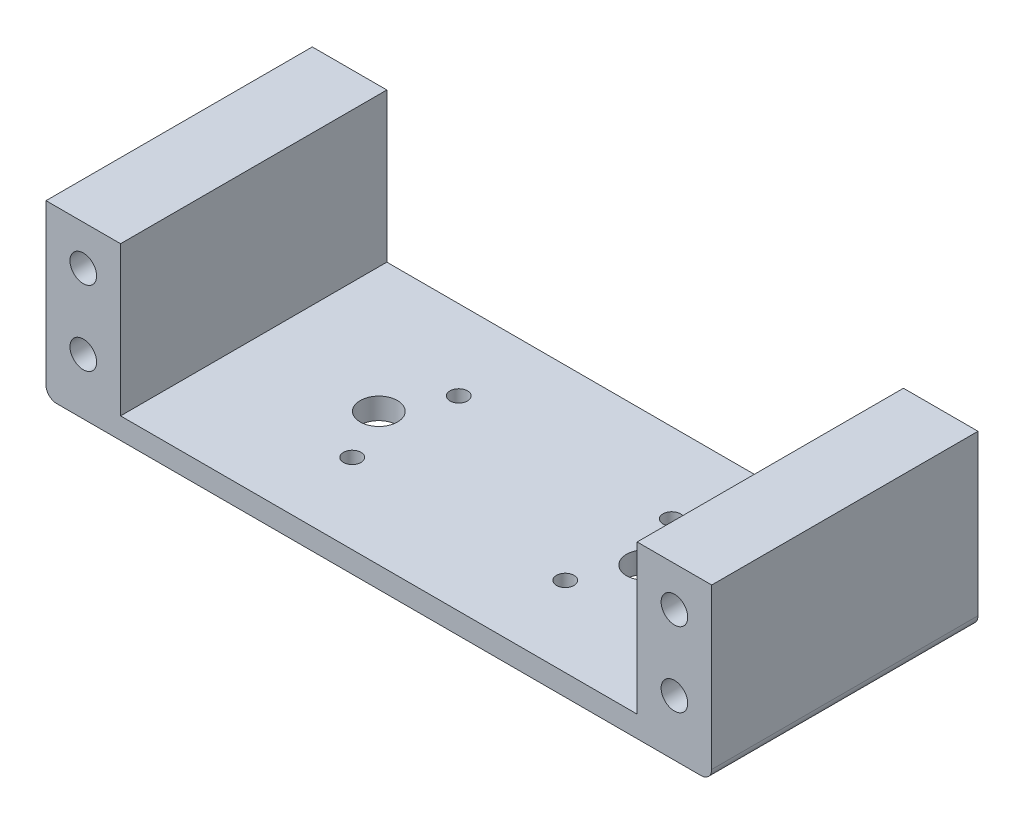
SolidWorks part; units mm, degrees
ref_plane "Front Plane" through (0, 0, 0) normal (0, 0, 1) x (1, 0, 0)
ref_plane "Top Plane" through (0, 0, 0) normal (0, 1, 0) x (1, 0, 0)
ref_plane "Right Plane" through (0, 0, 0) normal (1, 0, 0) x (0, 0, -1)
sketch "Sketch1" plane through (0, 0, 0) normal (0, 1, 0) x (1, 0, 0)
  line L1 (0, 0) -> (125, 0)
  line L2 (0, 0) -> (0, 50)
  line L3 (0, 50) -> (125, 50)
  line L4 (125, 0) -> (125, 50)
  dimension "D1" = 125
  dimension "D2" = 50
extrude "Boss-Extrude1" add sketch "Sketch1" along normal blind 4
sketch "Sketch2" plane through (0, 4, 0) normal (0, 1, 0) x (1, 0, 0)
  line L0 (0, 0) -> (125, 0) construction
  line L1 (0, 50) -> (14, 50)
  line L2 (0, 50) -> (0, 0)
  line L3 (0, 0) -> (14, 0)
  line L4 (14, 50) -> (14, 0)
  line L5 (125, 50) -> (0, 50) construction
  line L6 (125, 0) -> (111, 0)
  line L7 (125, 0) -> (125, 50)
  line L8 (125, 50) -> (111, 50)
  line L9 (111, 0) -> (111, 50)
  dimension "D1" = 14
  dimension "D2" = 14
extrude "Boss-Extrude2" add sketch "Sketch2" along normal blind 28
sketch "Sketch3" plane through (0, 0, 0) normal (0, 0, 1) x (1, 0, 0)
  line L0 (7, 32) -> (7, 0) construction
  line L1 (0, 32) -> (14, 32) construction
  line L2 (0, 0) -> (125, 0) construction
  line L3 (62.5, 0) -> (62.5, 4) construction
  line L4 (14, 4) -> (111, 4) construction
  circle A0 centre (7, 24.5) radius 2.5
  circle A1 centre (7, 10.5) radius 2.5
  circle A2 centre (118, 10.5) radius 2.5
  circle A3 centre (118, 24.5) radius 2.5
  dimension "D1" = 24.5
  dimension "D3" = 5
  dimension "D4" = 5
  dimension "D2" = 14
extrude "Cut-Extrude1" cut sketch "Sketch3" against normal blind 4.78
ref_plane "Plane1" through (0, 0, -25) normal (0, 0, 1) x (1, 0, 0)
mirror "Mirror1" about plane through (0, 0, -25) normal (0, 0, 1) of "Cut-Extrude1"
sketch "Sketch4" plane through (0, 0, 0) normal (0, -1, 0) x (1, 0, 0)
  line L0 (62.5, 0) -> (62.5, -50) construction
  line L1 (0, 0) -> (125, 0) construction
  line L2 (125, -50) -> (0, -50) construction
  line L3 (0, -25) -> (125, -25) construction
  line L4 (0, -50) -> (0, 0) construction
  line L5 (125, 0) -> (125, -50) construction
  circle A0 centre (82.5, -15) radius 1.65
  circle A1 centre (42.5, -15) radius 1.65
  circle A2 centre (82.5, -35) radius 1.65
  circle A3 centre (42.5, -35) radius 1.65
  circle A4 centre (37.5, -25) radius 3.5
  circle A5 centre (87.5, -25) radius 3.5
  dimension "D1" = 3.3
  dimension "D4" = 7
  dimension "D2" = 10
  dimension "D3" = 20
  dimension "D5" = 25
extrude "Cut-Extrude2" cut sketch "Sketch4" against normal through all
fillet "Fillet1" radius 2 2 edges at (125, 0, -25) (0, 0, -25)
